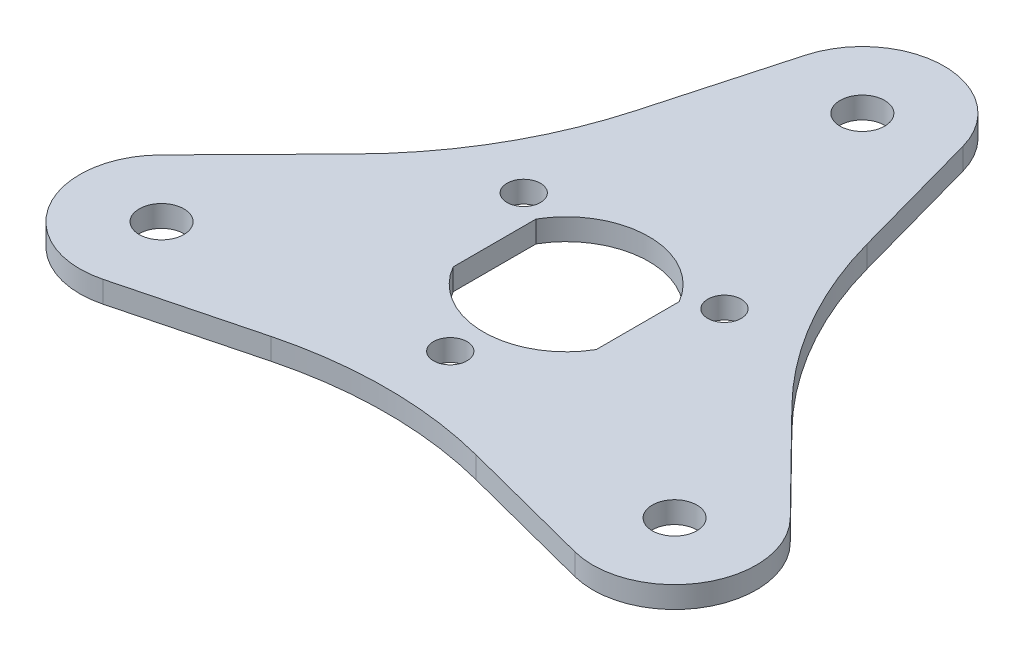
SolidWorks part; units mm, degrees
ref_plane "Front Plane" through (0, 0, 0) normal (0, 0, 1) x (1, 0, 0)
ref_plane "Top Plane" through (0, 0, 0) normal (0, 1, 0) x (1, 0, 0)
ref_plane "Right Plane" through (0, 0, 0) normal (1, 0, 0) x (0, 0, -1)
sketch "Sketch1" plane through (0, 0, 0) normal (0, 1, 0) x (1, 0, 0)
  line L0 (-9.625, 5.579) -> (-9.625, -5.579)
  line L1 (0, 39.8372) -> (-34.5, -19.9186) construction
  line L2 (-34.5, -19.9186) -> (34.5, -19.9186) construction
  line L3 (34.5, -19.9186) -> (0, 39.8372) construction
  line L4 (9.625, 5.579) -> (9.625, -5.579)
  line L5 (0, 0) -> (0, 39.8372) construction
  line L6 (-31.7431, -30.5675) -> (-13.7844, -25.9182)
  line L7 (0, -15.5885) -> (13.5, 7.7942) construction
  line L8 (13.5, 7.7942) -> (-13.5, 7.7942) construction
  line L9 (-13.5, 7.7942) -> (0, -15.5885) construction
  line L10 (13.7844, -25.9182) -> (31.7431, -30.5675)
  line L11 (-10.6007, 42.7741) -> (-15.5536, 24.8968)
  line L12 (-29.338, 1.0214) -> (-42.3438, -12.2066)
  line L13 (42.3438, -12.2066) -> (29.338, 1.0214)
  line L14 (15.5536, 24.8968) -> (10.6007, 42.7741)
  circle A0 centre (0, 0) radius 19.9186 construction
  circle A1 centre (0, 39.8372) radius 3
  circle A2 centre (-34.5, -19.9186) radius 3
  circle A3 centre (34.5, -19.9186) radius 3
  arc A4 (-9.625, -5.579) -> (9.625, -5.579) centre (0, 0) ccw
  arc A5 (9.625, 5.579) -> (-9.625, 5.579) centre (0, 0) ccw
  circle A6 centre (0, 0) radius 7.7942 construction
  circle A7 centre (0, -15.5885) radius 2.25
  circle A8 centre (-13.5, 7.7942) radius 2.25
  circle A9 centre (13.5, 7.7942) radius 2.25
  circle A10 centre (0, 39.8372) radius 11
  circle A12 centre (-34.5, -19.9186) radius 11
  circle A13 centre (34.5, -19.9186) radius 11
  arc A14 (-13.7844, -25.9182) -> (13.7844, -25.9182) centre (0, -79.1628) cw
  arc A15 (-15.5536, 24.8968) -> (-29.338, 1.0214) centre (-68.557, 39.5814) cw
  arc A16 (29.338, 1.0214) -> (15.5536, 24.8968) centre (68.557, 39.5814) cw
  dimension "D2" = 6
  dimension "D3" = 22.25
  dimension "D6" = 4.5
  dimension "D7" = 75
  dimension "D8" = 8
  dimension "D9" = 55
  dimension "D1" = 69
  dimension "D4" = 19.25
  dimension "D5" = 27
  dimension "D10" = 3
extrude "Boss-Extrude1" add sketch "Sketch1" along normal blind 2.9 contours L13 A16 L14 A10 L11 A15 L12 A12 L6 A14 L10 A13 A5 L4 A4 L0 A7 A8 A9 | A12 A2 | A13 A3 | A10 A1
